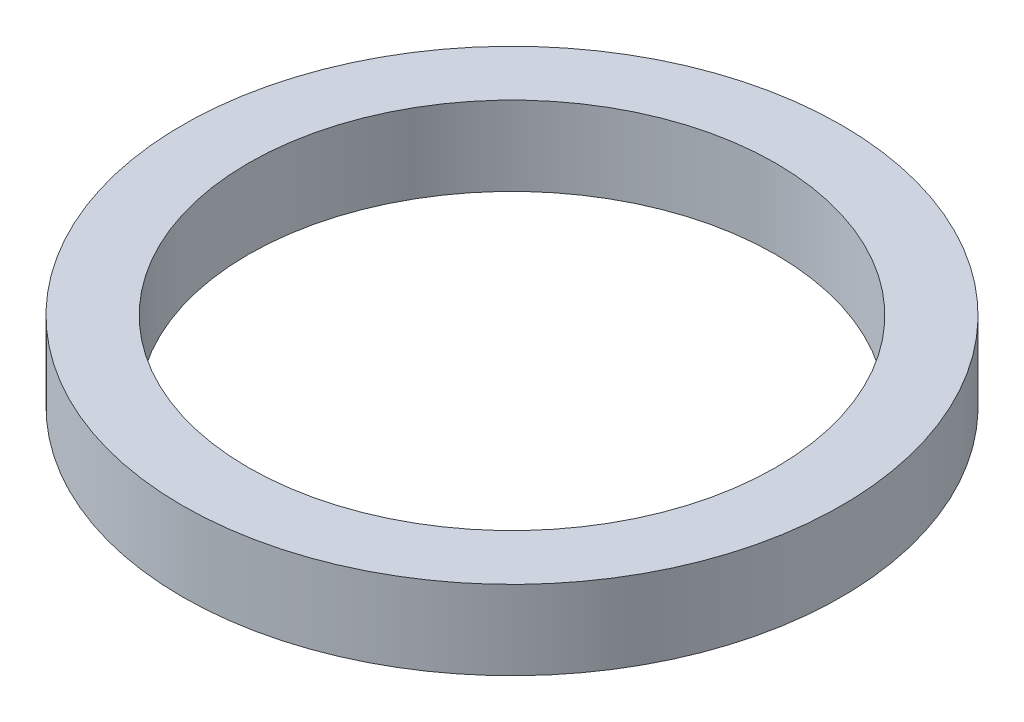
SolidWorks part; units mm, degrees
ref_plane "Front Plane" through (0, 0, 0) normal (0, 0, 1) x (1, 0, 0)
ref_plane "Top Plane" through (0, 0, 0) normal (0, 1, 0) x (1, 0, 0)
ref_plane "Right Plane" through (0, 0, 0) normal (1, 0, 0) x (0, 0, -1)
sketch "Sketch1" plane through (0, 0, 0) normal (0, 1, 0) x (1, 0, 0)
  circle A0 centre (0, 0) radius 20
  circle A1 centre (0, 0) radius 25
  dimension "D1" = 50
  dimension "D2" = 40
extrude "Boss-Extrude1" add sketch "Sketch1" along normal blind 6
